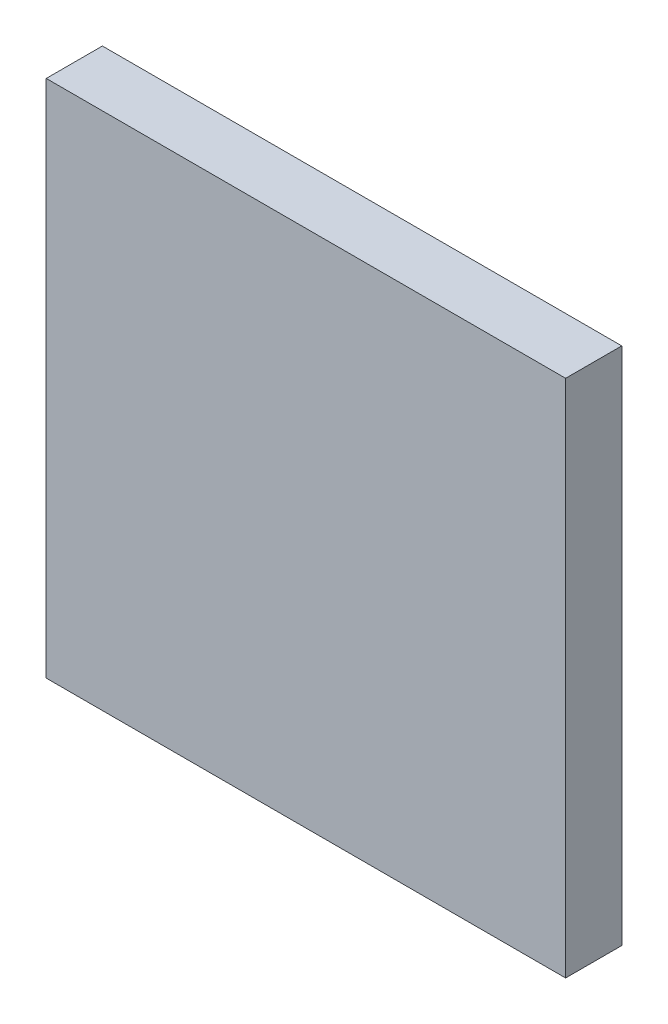
SolidWorks part; units mm, degrees
ref_plane "Plano frontal" through (0, 0, 0) normal (0, 0, 1) x (1, 0, 0)
ref_plane "Plano superior" through (0, 0, 0) normal (0, 1, 0) x (1, 0, 0)
ref_plane "Plano direito" through (0, 0, 0) normal (1, 0, 0) x (0, 0, -1)
sketch "Esboço1" plane through (0, 0, 0) normal (0, 0, 1) x (1, 0, 0)
  line L1 (-6.8941, 16.3185) -> (30.1059, 16.3185)
  line L2 (-6.8941, 16.3185) -> (-6.8941, -20.6815)
  line L3 (-6.8941, -20.6815) -> (30.1059, -20.6815)
  line L4 (30.1059, 16.3185) -> (30.1059, -20.6815)
  dimension "D1" = 37
  dimension "D2" = 37
extrude "Ressalto-extrusão1" add sketch "Esboço1" along normal blind 4
